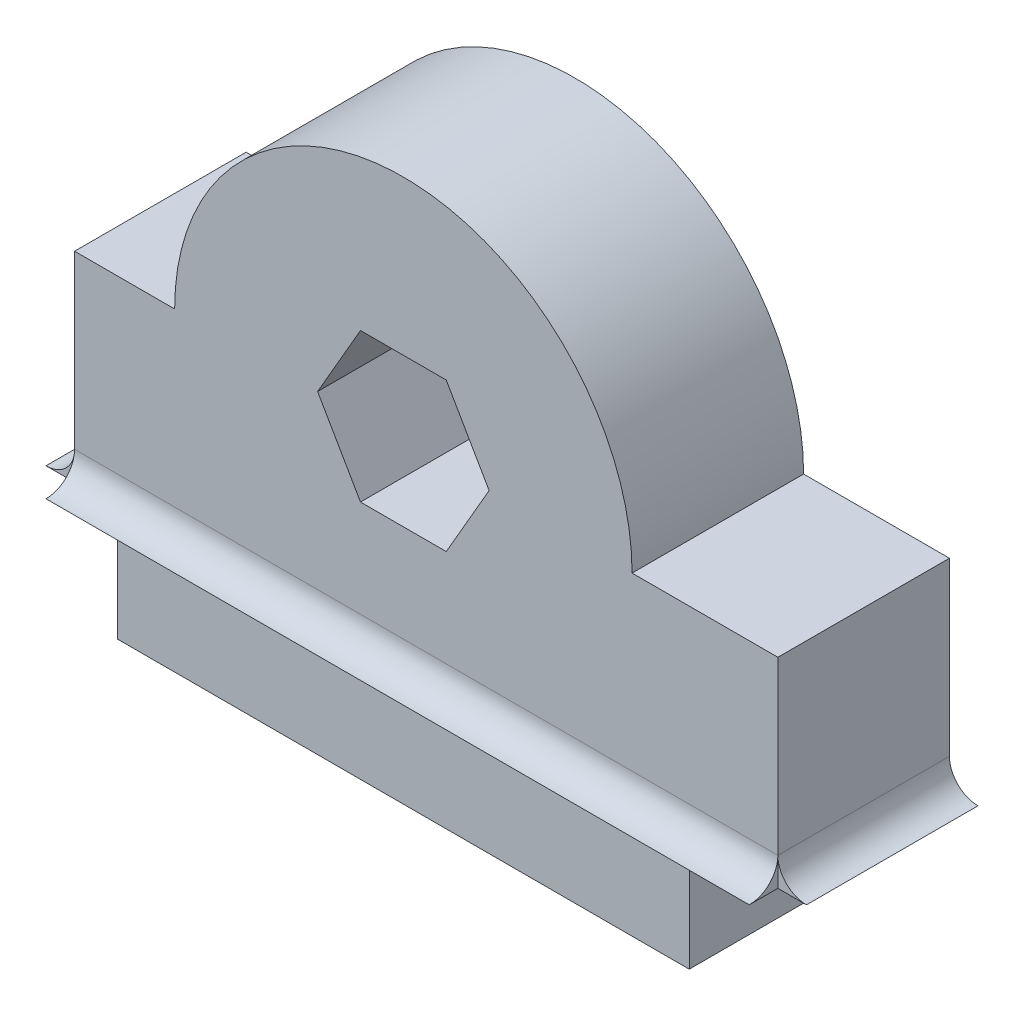
SolidWorks part; units mm, degrees
ref_plane "Front Plane" through (0, 0, 0) normal (0, 0, 1) x (1, 0, 0)
ref_plane "Top Plane" through (0, 0, 0) normal (0, 1, 0) x (1, 0, 0)
ref_plane "Right Plane" through (0, 0, 0) normal (1, 0, 0) x (0, 0, -1)
sketch "Sketch1" plane through (0, 0, 0) normal (0, 0, 1) x (1, 0, 0)
  line L0 (0, 0) -> (20, 0)
  line L1 (0, 0) -> (0, 4)
  line L2 (20, 0) -> (20, 4)
  line L3 (0, 4) -> (-1.5, 4)
  line L4 (23.1, 11) -> (23.1, 4)
  line L5 (-1.5, 4) -> (-1.5, 11)
  line L6 (-1.5, 11) -> (2, 11)
  line L7 (18, 11) -> (23.1, 11)
  line L8 (23.1, 4) -> (20, 4)
  line L11 (13, 11) -> (11.5, 13.5981)
  line L12 (11.5, 13.5981) -> (8.5, 13.5981)
  line L13 (8.5, 13.5981) -> (7, 11)
  line L14 (7, 11) -> (8.5, 8.4019)
  line L15 (8.5, 8.4019) -> (11.5, 8.4019)
  line L16 (11.5, 8.4019) -> (13, 11)
  arc A0 (18, 11) -> (2, 11) centre (10, 11) ccw
  dimension "D1" = 8
  dimension "D5" = 11.5
  dimension "D6" = 20
  dimension "D2" = 7
  dimension "D3" = 8.5
  dimension "D4" = 10
  dimension "D7" = 23.1
  dimension "D8" = 1.5
  dimension "D9" = 4
  dimension "D10" = 8.4019
extrude "Boss-Extrude1" add sketch "Sketch1" along normal blind 6
sketch "Sketch2" plane through (-1.5, 0, 0) normal (-1, 0, 0) x (0, 0, 1)
  line L0 (3, 0) -> (3, 7) construction
  line L1 (6, 4) -> (6, 5)
  line L2 (6, 4) -> (7, 4)
  line L3 (0, 4) -> (-1, 4) construction
  line L4 (0, 4) -> (0, 5) construction
  arc A0 (6, 5) -> (7, 4) centre (7, 5) ccw
  arc A1 (0, 5) -> (-1, 4) centre (-1, 5) cw construction
  dimension "D1" = 1
  dimension "D2" = 1
  dimension "D3" = 6
  dimension "D4" = 3
  dimension "D5" = 4
extrude "Boss-Extrude2" add sketch "Sketch2" against normal up to surface (24.6 mm away) up to face at (23.1, 7.5, 3)
sketch "Sketch4" plane through (0, 0, 6) normal (0, 0, 1) x (1, 0, 0)
  line L0 (10.8, 0) -> (10.8, 7) construction
  line L1 (23.1, 4) -> (23.1, 5)
  line L2 (23.1, 4) -> (24.1, 4)
  line L3 (-1.5, 4) -> (-2.5, 4)
  line L4 (-1.5, 4) -> (-1.5, 5)
  arc A0 (23.1, 5) -> (24.1, 4) centre (24.1, 5) ccw
  arc A1 (-1.5, 5) -> (-2.5, 4) centre (-2.5, 5) cw
  dimension "D1" = 1
  dimension "D2" = 1
  dimension "D3" = 10.8
  dimension "D4" = 12.3
  dimension "D5" = 4
extrude "Boss-Extrude3" add sketch "Sketch4" against normal up to surface (6 mm away) up to face at (10.32, 6.8, 0)
